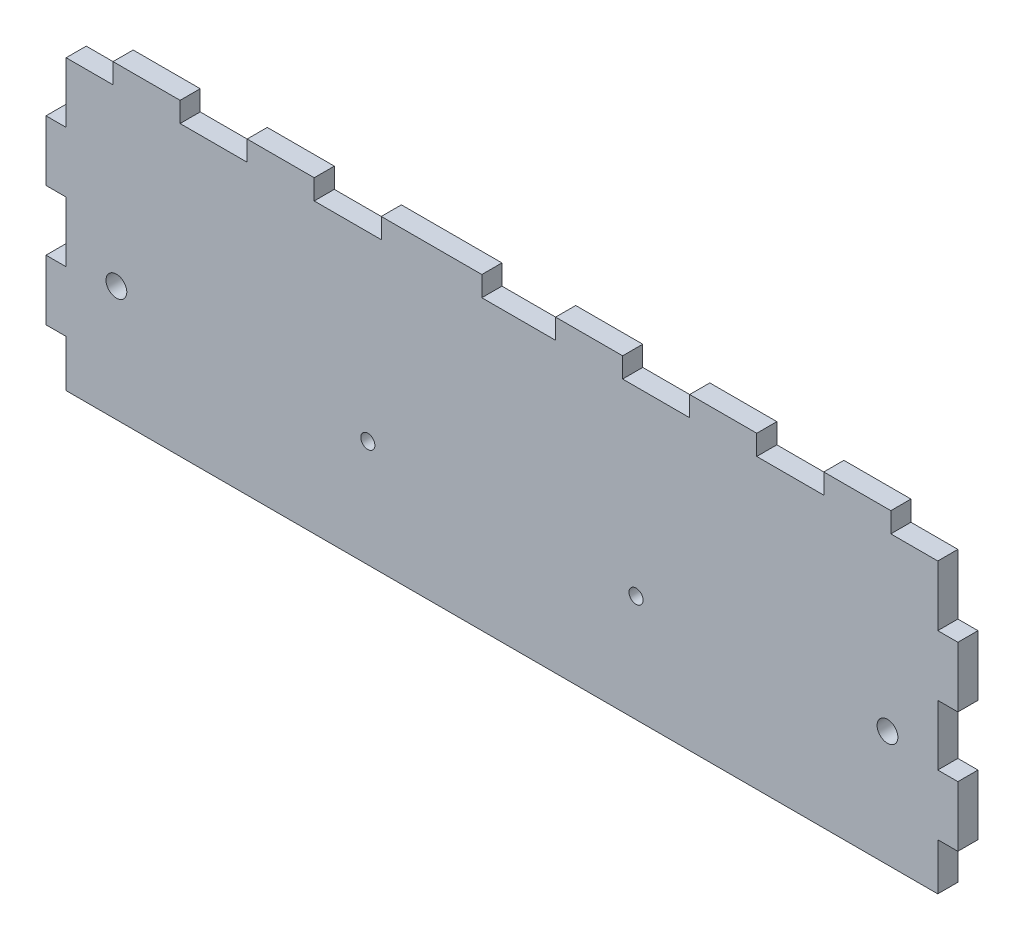
SolidWorks part; units mm, degrees
ref_plane "Front Plane" through (0, 0, 0) normal (0, 0, 1) x (1, 0, 0)
ref_plane "Top Plane" through (0, 0, 0) normal (0, 1, 0) x (1, 0, 0)
ref_plane "Right Plane" through (0, 0, 0) normal (1, 0, 0) x (0, 0, -1)
sketch "Sketch1" plane through (0, 0, 0) normal (0, 0, 1) x (1, 0, 0)
  line L4 (-136, 0) -> (0, 0)
  line L5 (0, 0) -> (0, 46)
  line L6 (0, 46) -> (-136, 46)
  line L7 (-136, 46) -> (-136, 0)
  line L8 (-136, 0) -> (0, 0)
  line L9 (0, 0) -> (0, 46)
  line L10 (0, 46) -> (-136, 46)
  line L11 (-136, 46) -> (-136, 0)
  circle A0 centre (-88, 15.95) radius 1.05 construction
  circle A1 centre (-125.5, 17.25) radius 1.55 construction
  circle A2 centre (-48, 15.95) radius 1.05 construction
  circle A3 centre (-10.5, 17.25) radius 1.55 construction
  circle A4 centre (-88, 15.95) radius 1.05
  circle A5 centre (-125.5, 17.25) radius 1.55
  circle A6 centre (-48, 15.95) radius 1.05
  circle A7 centre (-10.5, 17.25) radius 1.55
  dimension "D1" = 0
extrude "Boss-Extrude1" add sketch "Sketch1" along normal blind 3
sketch "Sketch2" plane through (0, 0, 3) normal (0, 0, 1) x (1, 0, 0)
  line L0 (-133, 43) -> (-133, 34) construction
  line L1 (-133, 34) -> (-136, 34) construction
  line L2 (-136, 34) -> (-136, 43) construction
  line L3 (-136, 43) -> (-133, 43) construction
  line L4 (-133, 25) -> (-133, 16) construction
  line L5 (-133, 16) -> (-136, 16) construction
  line L6 (-136, 16) -> (-136, 25) construction
  line L7 (-136, 25) -> (-133, 25) construction
  line L8 (-136, 0) -> (-136, 7) construction
  line L9 (-136, 7) -> (-133, 7) construction
  line L10 (-133, 7) -> (-133, 0) construction
  line L11 (-133, 0) -> (-136, 0) construction
  line L12 (-136, 46) -> (-126, 46) construction
  line L13 (-126, 46) -> (-126, 43) construction
  line L14 (-126, 43) -> (-136, 43) construction
  line L15 (-136, 43) -> (-136, 46) construction
  line L16 (-116, 46) -> (-106, 46) construction
  line L17 (-106, 46) -> (-106, 43) construction
  line L18 (-106, 43) -> (-116, 43) construction
  line L19 (-116, 43) -> (-116, 46) construction
  line L20 (-86, 43) -> (-96, 43) construction
  line L21 (-96, 43) -> (-96, 46) construction
  line L22 (-96, 46) -> (-86, 46) construction
  line L23 (-86, 46) -> (-86, 43) construction
  line L24 (-60, 43) -> (-71, 43) construction
  line L25 (-71, 43) -> (-71, 46) construction
  line L26 (-71, 46) -> (-60, 46) construction
  line L27 (-60, 46) -> (-60, 43) construction
  line L28 (-40, 43) -> (-50, 43) construction
  line L29 (-50, 43) -> (-50, 46) construction
  line L30 (-50, 46) -> (-40, 46) construction
  line L31 (-40, 46) -> (-40, 43) construction
  line L32 (-20, 43) -> (-30, 43) construction
  line L33 (-30, 43) -> (-30, 46) construction
  line L34 (-30, 46) -> (-20, 46) construction
  line L35 (-20, 46) -> (-20, 43) construction
  line L36 (0, 43) -> (-10, 43) construction
  line L37 (-10, 43) -> (-10, 46) construction
  line L38 (-10, 46) -> (0, 46) construction
  line L39 (0, 46) -> (0, 43) construction
  line L40 (0, 43) -> (0, 34) construction
  line L41 (0, 34) -> (-3, 34) construction
  line L42 (-3, 34) -> (-3, 43) construction
  line L43 (-3, 43) -> (0, 43) construction
  line L44 (0, 25) -> (0, 16) construction
  line L45 (0, 16) -> (-3, 16) construction
  line L46 (-3, 16) -> (-3, 25) construction
  line L47 (-3, 25) -> (0, 25) construction
  line L48 (-3, 0) -> (-3, 7) construction
  line L49 (-3, 7) -> (0, 7) construction
  line L50 (0, 7) -> (0, 0) construction
  line L51 (0, 0) -> (-3, 0) construction
  line L52 (-133, 43) -> (-133, 34)
  line L53 (-133, 34) -> (-136, 34)
  line L54 (-136, 34) -> (-136, 43)
  line L55 (-136, 43) -> (-133, 43)
  line L56 (-133, 25) -> (-133, 16)
  line L57 (-133, 16) -> (-136, 16)
  line L58 (-136, 16) -> (-136, 25)
  line L59 (-136, 25) -> (-133, 25)
  line L60 (-136, 0) -> (-136, 7)
  line L61 (-136, 7) -> (-133, 7)
  line L62 (-133, 7) -> (-133, 0)
  line L63 (-133, 0) -> (-136, 0)
  line L64 (-136, 46) -> (-126, 46)
  line L65 (-126, 46) -> (-126, 43)
  line L66 (-126, 43) -> (-136, 43)
  line L67 (-136, 43) -> (-136, 46)
  line L68 (-116, 46) -> (-106, 46)
  line L69 (-106, 46) -> (-106, 43)
  line L70 (-106, 43) -> (-116, 43)
  line L71 (-116, 43) -> (-116, 46)
  line L72 (-86, 43) -> (-96, 43)
  line L73 (-96, 43) -> (-96, 46)
  line L74 (-96, 46) -> (-86, 46)
  line L75 (-86, 46) -> (-86, 43)
  line L76 (-60, 43) -> (-71, 43)
  line L77 (-71, 43) -> (-71, 46)
  line L78 (-71, 46) -> (-60, 46)
  line L79 (-60, 46) -> (-60, 43)
  line L80 (-40, 43) -> (-50, 43)
  line L81 (-50, 43) -> (-50, 46)
  line L82 (-50, 46) -> (-40, 46)
  line L83 (-40, 46) -> (-40, 43)
  line L84 (-20, 43) -> (-30, 43)
  line L85 (-30, 43) -> (-30, 46)
  line L86 (-30, 46) -> (-20, 46)
  line L87 (-20, 46) -> (-20, 43)
  line L88 (0, 43) -> (-10, 43)
  line L89 (-10, 43) -> (-10, 46)
  line L90 (-10, 46) -> (0, 46)
  line L91 (0, 46) -> (0, 43)
  line L92 (0, 43) -> (0, 34)
  line L93 (0, 34) -> (-3, 34)
  line L94 (-3, 34) -> (-3, 43)
  line L95 (-3, 43) -> (0, 43)
  line L96 (0, 25) -> (0, 16)
  line L97 (0, 16) -> (-3, 16)
  line L98 (-3, 16) -> (-3, 25)
  line L99 (-3, 25) -> (0, 25)
  line L100 (-3, 0) -> (-3, 7)
  line L101 (-3, 7) -> (0, 7)
  line L102 (0, 7) -> (0, 0)
  line L103 (0, 0) -> (-3, 0)
  line M3 (-136, 46) -> (-136, 0)
  line M4 (-136, 0) -> (0, 0)
  line M5 (0, 0) -> (0, 46)
  line M6 (0, 46) -> (-136, 46)
extrude "Cut-Extrude1" cut sketch "Sketch2" against normal up to next contours L79 L77 L76 M6 | L75 L73 L72 M6 | L71 L70 L69 M6 | L66 L65 L55 M6 M3 | L55 L53 L52 M3 | L59 L57 L56 M3 | L62 L61 M3 M4 | L101 L100 M4 M5 | L99 L98 L97 M5 | L94 L93 L88 M5 | L89 L88 M5 M6 | L87 L85 L84 M6 | L83 L81 L80 M6
